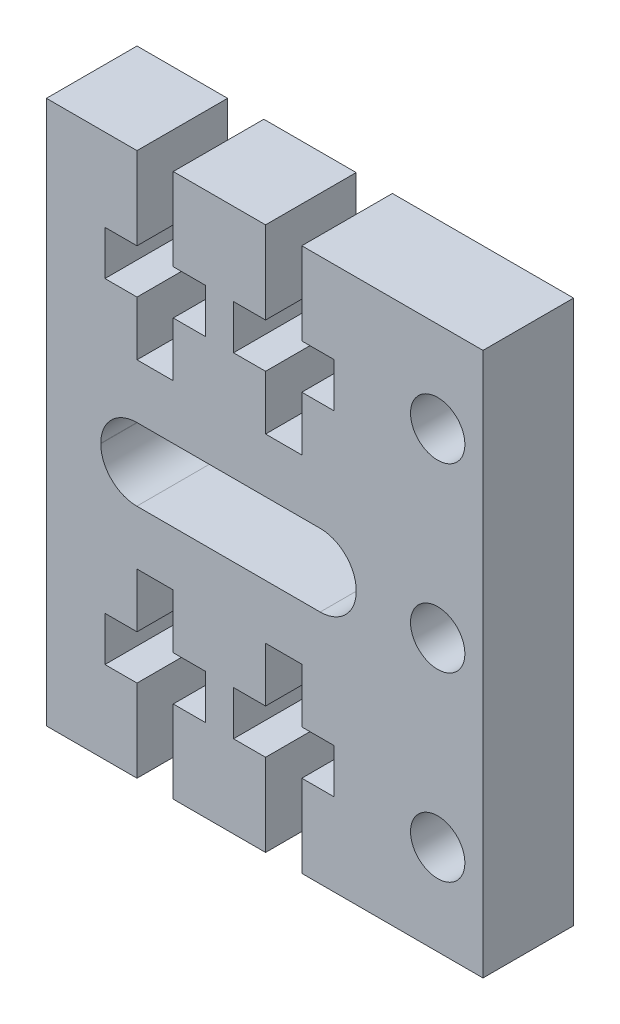
SolidWorks part; units mm, degrees
material "Acrílico (médio-alto impacto)"
ref_plane "Plano frontal" through (0, 0, 0) normal (0, 0, 1) x (1, 0, 0)
ref_plane "Plano superior" through (0, 0, 0) normal (0, 1, 0) x (1, 0, 0)
ref_plane "Plano direito" through (0, 0, 0) normal (1, 0, 0) x (0, 0, -1)
sketch "Esboço1" plane through (0, 0, 0) normal (0, 0, 1) x (1, 0, 0)
  line L1 (-20.5249, -15.4595) -> (3.5711, -15.4595)
  line L2 (-20.5249, -15.4595) -> (-20.5249, -45.4595)
  line L3 (-20.5249, -45.4595) -> (3.5711, -45.4595)
  line L4 (3.5711, -15.4595) -> (3.5711, -45.4595)
  dimension "D1" = 24.096
  dimension "D2" = 30
extrude "Ressalto-extrusão1" add sketch "Esboço1" along normal blind 5
sketch "Esboço2" plane through (0, 0, 0) normal (0, 0, -1) x (-1, 0, 0)
  line L0 (-3.5711, -45.4595) -> (-3.5711, -15.4595) construction
  line L2 (-3.5711, -15.4595) -> (20.5249, -15.4595) construction
  circle A0 centre (-1.0711, -30.4595) radius 1.5
  circle A1 centre (-1.0711, -20.4595) radius 1.5
  dimension "D1" = 3
  dimension "D2" = 3
  dimension "D3" = 2.5
  dimension "D4" = 10
  dimension "D5" = 5
  dimension "D6" = 2.5
extrude "Corte-extrusão1" cut sketch "Esboço2" against normal blind 10
sketch "Esboço3" plane through (0, 0, 0) normal (0, 0, -1) x (-1, 0, 0)
  line L0 (-3.5711, -15.4595) -> (20.5249, -15.4595) construction
  line L1 (15.5249, -15.4595) -> (13.5249, -15.4595)
  line L2 (15.5249, -15.4595) -> (15.5249, -20.0095)
  line L3 (15.5249, -25.4595) -> (13.5249, -25.4595)
  line L4 (13.5249, -15.4595) -> (13.5249, -20.0095)
  line L5 (20.5249, -15.4595) -> (20.5249, -45.4595) construction
  line L6 (8.4289, -15.4595) -> (6.4289, -15.4595)
  line L7 (8.4289, -15.4595) -> (8.4289, -20.0095)
  line L8 (8.4289, -25.4595) -> (6.4289, -25.4595)
  line L9 (6.4289, -15.4595) -> (6.4289, -20.0095)
  line L10 (-3.5711, -45.4595) -> (-3.5711, -15.4595) construction
  line L11 (15.5249, -22.4595) -> (15.5249, -25.4595)
  line L12 (17.2949, -22.4595) -> (15.5249, -22.4595)
  line L13 (17.2949, -22.4595) -> (17.2949, -20.0095)
  line L14 (17.2949, -20.0095) -> (15.5249, -20.0095)
  line L15 (11.7549, -22.4595) -> (11.7549, -20.0095)
  line L16 (10.1989, -22.4595) -> (8.4289, -22.4595)
  line L17 (10.1989, -22.4595) -> (10.1989, -20.0095)
  line L18 (10.1989, -20.0095) -> (8.4289, -20.0095)
  line L19 (4.6589, -22.4595) -> (4.6589, -20.0095)
  line L20 (13.5249, -22.4595) -> (13.5249, -25.4595)
  line L21 (13.5249, -22.4595) -> (11.7549, -22.4595)
  line L22 (13.5249, -20.0095) -> (11.7549, -20.0095)
  line L23 (8.4289, -22.4595) -> (8.4289, -25.4595)
  line L24 (6.4289, -22.4595) -> (6.4289, -25.4595)
  line L25 (6.4289, -22.4595) -> (4.6589, -22.4595)
  line L26 (6.4289, -20.0095) -> (4.6589, -20.0095)
  line L27 (20.5249, -30.4595) -> (14.8342, -30.4595) construction
  line L28 (6.4289, -40.9095) -> (4.6589, -40.9095)
  line L29 (6.4289, -38.4595) -> (4.6589, -38.4595)
  line L30 (6.4289, -38.4595) -> (6.4289, -35.4595)
  line L31 (8.4289, -38.4595) -> (8.4289, -35.4595)
  line L32 (13.5249, -40.9095) -> (11.7549, -40.9095)
  line L33 (13.5249, -38.4595) -> (11.7549, -38.4595)
  line L34 (13.5249, -38.4595) -> (13.5249, -35.4595)
  line L35 (4.6589, -38.4595) -> (4.6589, -40.9095)
  line L36 (10.1989, -40.9095) -> (8.4289, -40.9095)
  line L37 (10.1989, -38.4595) -> (10.1989, -40.9095)
  line L38 (10.1989, -38.4595) -> (8.4289, -38.4595)
  line L39 (11.7549, -38.4595) -> (11.7549, -40.9095)
  line L40 (17.2949, -40.9095) -> (15.5249, -40.9095)
  line L41 (17.2949, -38.4595) -> (17.2949, -40.9095)
  line L42 (17.2949, -38.4595) -> (15.5249, -38.4595)
  line L43 (15.5249, -38.4595) -> (15.5249, -35.4595)
  line L44 (6.4289, -45.4595) -> (6.4289, -40.9095)
  line L45 (8.4289, -35.4595) -> (6.4289, -35.4595)
  line L46 (8.4289, -45.4595) -> (8.4289, -40.9095)
  line L47 (8.4289, -45.4595) -> (6.4289, -45.4595)
  line L48 (13.5249, -45.4595) -> (13.5249, -40.9095)
  line L49 (15.5249, -35.4595) -> (13.5249, -35.4595)
  line L50 (15.5249, -45.4595) -> (15.5249, -40.9095)
  line L51 (15.5249, -45.4595) -> (13.5249, -45.4595)
  dimension "D1" = 10
  dimension "D2" = 10
  dimension "D3" = 2
  dimension "D4" = 2
  dimension "D5" = 5
  dimension "D6" = 10
  dimension "D7" = 5.54
  dimension "D8" = 2.45
  dimension "D9" = 5.54
  dimension "D10" = 2.45
  dimension "D11" = 1.77
  dimension "D12" = 1.77
  dimension "D13" = 1.77
  dimension "D14" = 1.77
  dimension "D15" = 3
  dimension "D16" = 3
extrude "Corte-extrusão2" cut sketch "Esboço3" against normal through all
sketch "Esboço4" plane through (0, 0, 0) normal (0, 0, -1) x (-1, 0, 0)
  line L0 (20.5249, -15.4595) -> (20.5249, -45.4595) construction
  line L1 (15.5349, -32.4595) -> (5.4153, -32.4595)
  line L2 (17.5249, -30.4695) -> (17.5249, -30.4495)
  line L3 (15.5349, -28.4595) -> (5.4153, -28.4595)
  line L4 (3.4253, -30.4695) -> (3.4253, -30.4495)
  line L5 (-3.5711, -45.4595) -> (-3.5711, -15.4595) construction
  line L6 (6.4289, -45.4595) -> (-3.5711, -45.4595) construction
  line L7 (-3.5711, -15.4595) -> (6.4289, -15.4595) construction
  arc A0 (5.4153, -28.4595) -> (3.4253, -30.4495) centre (5.4153, -30.4495) ccw
  arc A1 (5.4153, -32.4595) -> (3.4253, -30.4695) centre (5.4153, -30.4695) cw
  arc A2 (15.5349, -32.4595) -> (17.5249, -30.4695) centre (15.5349, -30.4695) ccw
  arc A3 (17.5249, -30.4495) -> (15.5349, -28.4595) centre (15.5349, -30.4495) ccw
  dimension "D5" = 1.99
  dimension "D1" = 3
  dimension "D2" = 6.9964
  dimension "D3" = 13
  dimension "D4" = 13
extrude "Corte-extrusão3" cut sketch "Esboço4" against normal blind 10
sketch "Esboço5" plane through (0, 0, 5) normal (0, 0, 1) x (1, 0, 0)
  line L0 (-6.4289, -45.4595) -> (3.5711, -45.4595) construction
  line L1 (3.5711, -45.4595) -> (3.5711, -15.4595) construction
  circle A0 centre (1.0711, -40.4595) radius 1.5
  dimension "D1" = 5
  dimension "D2" = 2.5
  dimension "D3" = 3
extrude "Corte-extrusão4" cut sketch "Esboço5" against normal through all
